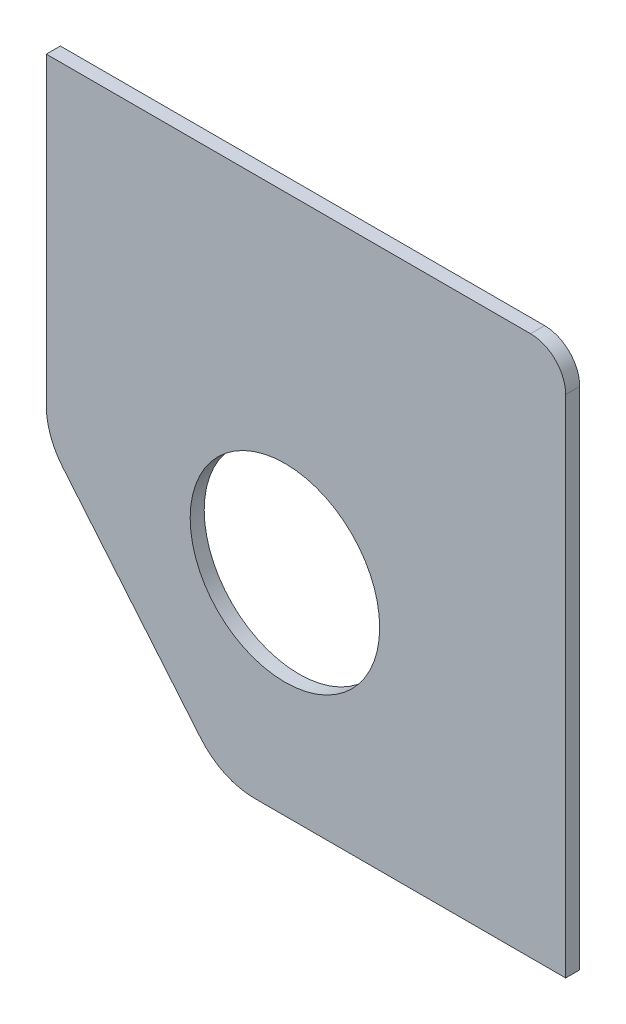
SolidWorks part; units mm, degrees
ref_plane "Plano frontal" through (0, 0, 0) normal (0, 0, 1) x (1, 0, 0)
ref_plane "Plano superior" through (0, 0, 0) normal (0, 1, 0) x (1, 0, 0)
ref_plane "Plano direito" through (0, 0, 0) normal (1, 0, 0) x (0, 0, -1)
sketch "Esboço1" plane through (0, 0, 0) normal (0, 0, 1) x (1, 0, 0)
  line L1 (-39.6949, 28.8545) -> (34.3051, 28.8545)
  line L2 (-39.6949, 28.8545) -> (-39.6949, -48.1455)
  line L3 (-39.6949, -48.1455) -> (34.3051, -48.1455)
  line L4 (34.3051, 28.8545) -> (34.3051, -48.1455)
  dimension "D1" = 74
  dimension "D2" = 77
extrude "Ressalto-extrusão1" add sketch "Esboço1" along normal blind 2
sketch "Esboço2" plane through (0, 0, 2) normal (0, 0, 1) x (1, 0, 0)
  line L0 (-39.6949, 28.8545) -> (-39.6949, -48.1455) construction
  circle A0 centre (-5.6949, -18.1455) radius 13.5
  dimension "D1" = 27
  dimension "D2" = 34
  dimension "D3" = 30
extrude "Corte-extrusão2" cut sketch "Esboço2" against normal blind 2
sketch "Esboço3" plane through (0, 0, 2) normal (0, 0, 1) x (1, 0, 0)
  line L0 (-39.6949, -18.1455) -> (-14.6949, -48.1455)
  line L1 (-39.6949, 28.8545) -> (-39.6949, -48.1455) construction
  line L2 (-39.6949, -48.1455) -> (34.3051, -48.1455) construction
  dimension "D1" = 30
  dimension "D2" = 25
extrude "Corte-extrusão4" cut sketch "Esboço3" against normal through all and the other way through all flip side to cut
fillet "Filete1" radius 5 1 edges at (34.3051, 28.8545, 1)
fillet "Filete3" radius 10 1 edges at (-39.6949, -18.1455, 1)
fillet "Filete4" radius 10 1 edges at (-14.6949, -48.1455, 1)
